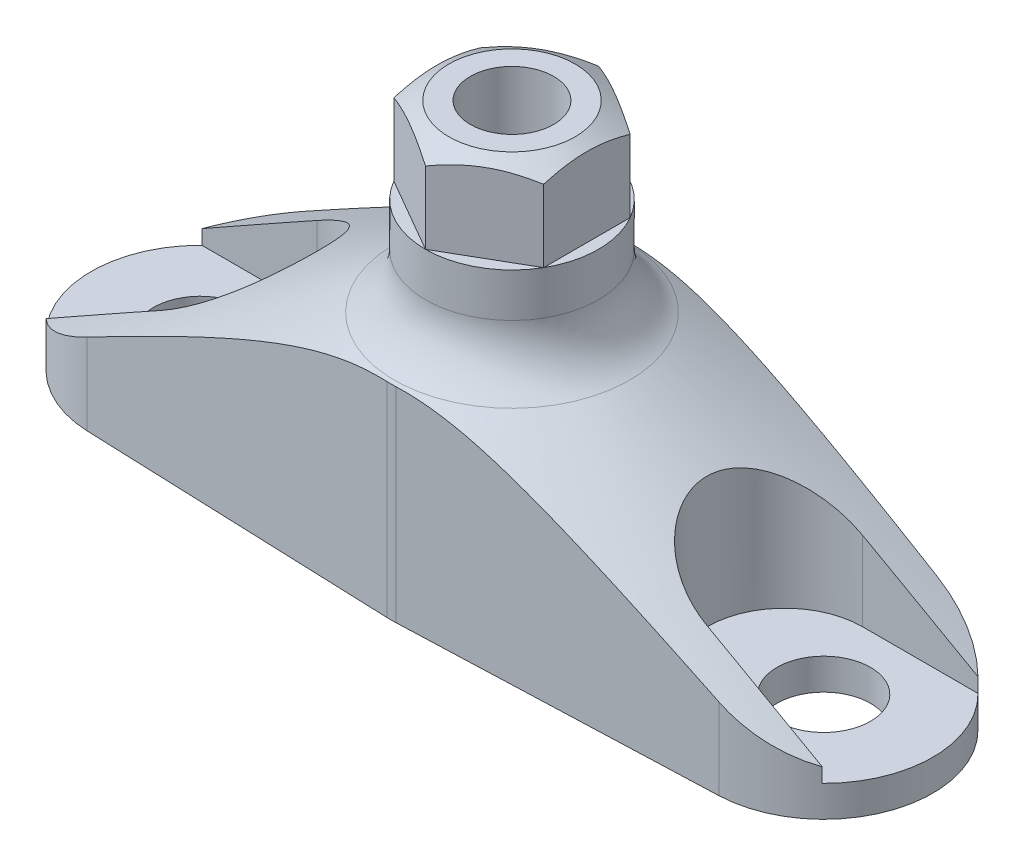
SolidWorks part; units mm, degrees
ref_plane "Płaszczyzna XY" through (0, 0, 0) normal (0, 0, 1) x (1, 0, 0)
ref_plane "Płaszczyzna XZ" through (0, 0, 0) normal (0, 1, 0) x (1, 0, 0)
ref_plane "Płaszczyzna YZ" through (0, 0, 0) normal (1, 0, 0) x (0, 0, -1)
sketch "Szkic1" plane through (0, 0, 0) normal (0, 0, 1) x (1, 0, 0)
  line L0 (0, 0) -> (0, 25) construction
  line L1 (0, 0) -> (0, 25)
  line L2 (0, 0) -> (27, 0)
  line L4 (0, 25) -> (27, 25)
  line L5 (27, 0) -> (27, 25)
  dimension "D1" = 54
  dimension "D2" = 25
revolve "Obrót1" add sketch "Szkic1" angle 360 about L0
sketch "Szkic2" plane through (0, 0, 0) normal (0, 0, 1) x (1, 0, 0)
  line L0 (0, 0) -> (0, 25) construction
  line L1 (27, 25) -> (-27, 25) construction
  line L2 (0, 25) -> (5.55, 25) construction
  line L3 (5.55, 25) -> (5.55, 14.3842)
  line L4 (5.55, 14.3842) -> (27, 2)
  line L5 (27, 0) -> (27, 25) construction
  line L6 (-27, 0) -> (27, 0) construction
  line L7 (5.55, 25) -> (27, 25)
  line L8 (27, 25) -> (27, 2)
  dimension "D1" = 2
  dimension "D2" = 30
  dimension "D3" = 11.1
revolve "Wycięcie-obrót1" cut sketch "Szkic2" angle 360 about L0
fillet "Zaokrąglenie1" radius 4 1 edges at (0, 14.3842, -5.55)
ref_plane "Płaszczyzna1" through (0, 2, 0) normal (0, 1, 0) x (1, 0, 0)
sketch "Szkic4" plane through (0, 2, 0) normal (0, 1, 0) x (1, 0, 0)
  line L0 (0, 8.8242) -> (0, -11.1289) construction
  circle A0 centre (-20, 0) radius 3
  circle A1 centre (20, 0) radius 3
  dimension "D1" = 6
  dimension "D2" = 6
  dimension "D3" = 40
extrude "Wytnij-wyciągnięcie3" cut sketch "Szkic4" against normal through all and the other way through all
sketch "Szkic3" plane through (0, 2, 0) normal (0, 1, 0) x (1, 0, 0)
  line L0 (-17.5, 5) -> (-26.533, 5)
  line L13 (-17.5, -5) -> (-26.533, -5)
  line L14 (17.5, 5) -> (26.533, 5)
  line L15 (17.5, -5) -> (26.533, -5)
  line L16 (0, 21.1527) -> (0, -20.0817) construction
  arc A1 (-17.5, -5) -> (-17.5, 5) centre (-17.5, 0) ccw
  arc A2 (17.5, 5) -> (17.5, -5) centre (17.5, 0) ccw
  circle A3 centre (0, 0) radius 27 construction
  arc A4 (-26.533, 5) -> (-26.533, -5) centre (0, 0) ccw
  arc A5 (26.533, -5) -> (26.533, 5) centre (0, 0) ccw
  dimension "D1" = 10
  dimension "D2" = 10
  dimension "D3" = 35
extrude "Wytnij-wyciągnięcie2" cut sketch "Szkic3" along normal through all
sketch "Szkic5" plane through (0, 0, 0) normal (0, -1, 0) x (1, 0, 0)
  line L0 (-20.2625, 6.9951) -> (-0.2906, 7.7445)
  line L1 (-20.2625, -6.9951) -> (-0.2906, -7.7445)
  line L2 (0.2906, 7.7445) -> (20.2625, 6.9951)
  line L3 (20.2625, -6.9951) -> (0.2906, -7.7445)
  arc A0 (-0.2906, -7.7445) -> (0.2906, -7.7445) centre (0, 0) ccw
  arc A1 (-20.2625, 6.9951) -> (-20.2625, -6.9951) centre (-20, 0) ccw
  arc A2 (20.2625, -6.9951) -> (20.2625, 6.9951) centre (20, 0) ccw
  circle A3 centre (0, 0) radius 27 construction
  arc A4 (0.2906, 7.7445) -> (-0.2906, 7.7445) centre (0, 0) ccw
  dimension "D1" = 15.5
extrude "Wytnij-wyciągnięcie4" cut sketch "Szkic5" against normal through all flip side to cut
sketch "Szkic6" plane through (0, 25, 0) normal (0, 1, 0) x (1, 0, 0)
  circle A0 centre (0, 0) radius 2.675
  dimension "D1" = 5.35
extrude "Wytnij-wyciągnięcie5" cut sketch "Szkic6" against normal through all
sketch "Szkic7" plane through (0, 25, 0) normal (0, 1, 0) x (1, 0, 0)
  line L1 (-4.8064, 2.775) -> (-4.8064, -2.775)
  line L2 (-4.8064, -2.775) -> (0, -5.55)
  line L3 (0, -5.55) -> (4.8064, -2.775)
  line L4 (4.8064, -2.775) -> (4.8064, 2.775)
  line L5 (4.8064, 2.775) -> (0, 5.55)
  line L6 (0, 5.55) -> (-4.8064, 2.775)
  circle A0 centre (0, 0) radius 4.8064 construction
  circle A1 centre (0, 0) radius 5.55 construction
extrude "Wytnij-wyciągnięcie6" cut sketch "Szkic7" against normal blind 5.5 flip side to cut
sketch "Szkic9" plane through (0, 0, 0) normal (0, 0, 1) x (1, 0, 0)
  line L0 (4.05, 25) -> (5.55, 24.134)
  line L1 (5.55, 24.134) -> (5.55, 25)
  line L2 (5.55, 25) -> (4.05, 25)
  line L3 (5.55, 16.6936) -> (5.55, 19.5) construction
  line L4 (5.55, 16.6936) -> (5.55, 19.5) construction
  line L5 (0, 25) -> (4.8064, 25) construction
  line L6 (0, 19.5) -> (0, 25) construction
  line L7 (0, 19.5) -> (0, 25) construction
  dimension "D1" = 30
  dimension "D2" = 1.5
revolve "Wycięcie-obrót2" cut sketch "Szkic9" angle 360 about L7
equation "\"D3@Szkic3\"=40-2*1/2*5"
